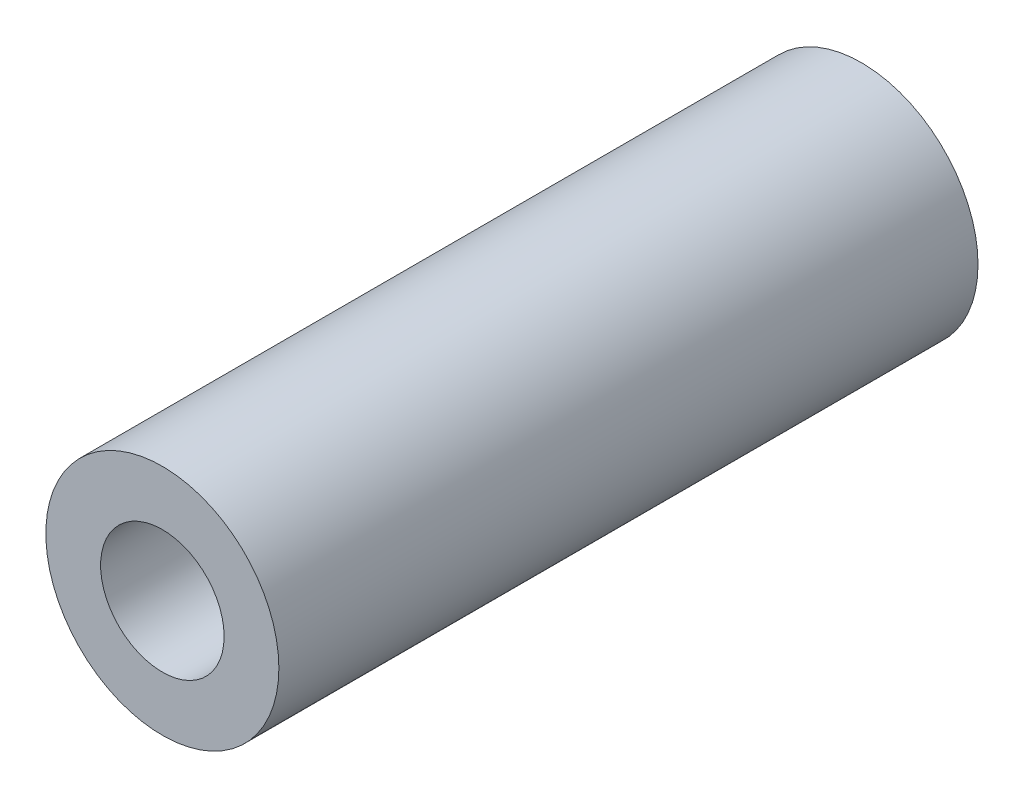
SolidWorks part; units mm, degrees
ref_plane "Front Plane" through (0, 0, 0) normal (0, 0, 1) x (1, 0, 0)
ref_plane "Top Plane" through (0, 0, 0) normal (0, 1, 0) x (1, 0, 0)
ref_plane "Right Plane" through (0, 0, 0) normal (1, 0, 0) x (0, 0, -1)
sketch "Sketch1" plane through (0, 0, 0) normal (0, 0, 1) x (1, 0, 0)
  circle A0 centre (0, 0) radius 5
  circle A1 centre (0, 0) radius 2.65
  dimension "OD" = 10
  dimension "ID" = 5.3
extrude "Extrude1" add sketch "Sketch1" along normal mid plane 30
sketch "Sketch2" plane through (0, 0, 0) normal (1, 0, 0) x (0, 0, -1)
  line L0 (-15, -2.65) -> (15, -2.65) construction
  line L3 (15, 2.65) -> (-15, 2.65) construction
  line L5 (-15, -2.65) -> (15, -2.65)
  line L6 (15, 2.65) -> (-15, 2.65)
sketch "Sketch4" plane through (0, 0, 15) normal (0, 0, 1) x (1, 0, 0)
  line L0 (0, 0) -> (-1.8738, 1.8738)
  line L1 (0, -5.5) -> (0, 5.5) construction
  circle A0 centre (0, 0) radius 2.65 construction
  dimension "D1" = 45
